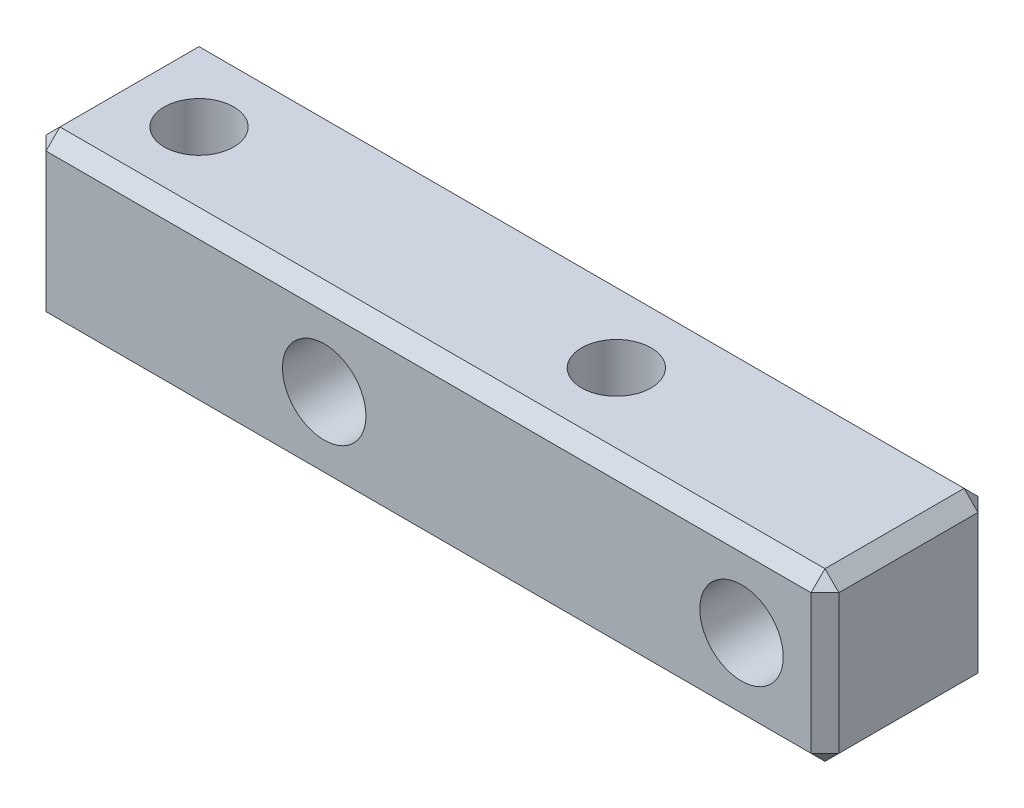
SolidWorks part; units mm, degrees
material "6061 合金"
ref_plane "前视基准面" through (0, 0, 0) normal (0, 0, 1) x (1, 0, 0)
ref_plane "上视基准面" through (0, 0, 0) normal (0, 1, 0) x (1, 0, 0)
ref_plane "右视基准面" through (0, 0, 0) normal (1, 0, 0) x (0, 0, -1)
sketch "草图2" plane through (0, 0, 0) normal (0, 0, 1) x (1, 0, 0)
  line L10 (3, 3) -> (3, -3)
  line L11 (0, 0) -> (-15, 0) construction
  line L41 (3, -3) -> (-25.5, -3)
  line L48 (-25.5, 3) -> (3, 3)
  line L49 (-25.5, 3) -> (-25.5, -3)
  circle A3 centre (-15, 0) radius 1.5
  circle A5 centre (0, 0) radius 1.5
  dimension "D1" = 15
  dimension "D2" = 3
  dimension "D3" = 3
  dimension "D4" = 10.5
  dimension "D7" = 3
  dimension "D6" = 3
extrude "凸台-拉伸1" add sketch "草图2" along normal mid plane 6
hole_wizard "M3 螺纹孔1" [suppressed] positions "草图5" profile "草图4" tap size "M3" standard "GB"
sketch "草图5" plane through (0, 0, 3) normal (0, 0, 1) x (1, 0, 0)
  point P0 (0, 0)
  point P3 (-15, 0)
sketch "草图4" plane through (0, 0, 3) normal (1, 0, 0) x (0, -1, 0)
  line L0 (0, 0) -> (0, 6)
  line L1 (0, 6) -> (1.25, 6)
  line L2 (1.25, 6) -> (1.25, 0)
  line L5 (1.25, 0) -> (0, 0)
  line L11 (0, -6.35) -> (0, 107.95) construction
  dimension "通孔螺纹孔钻头直径" = 2.5
  dimension "通孔螺纹孔钻头深度" = 6
hole_wizard "M3 螺纹孔2" positions "草图6" profile "草图7" tap size "M3" standard "GB" end condition through all
sketch "草图6" plane through (0, 3, 0) normal (0, 1, 0) x (1, 0, 0)
  line L1 (-22.5, 0) -> (0, 0) construction
  line L2 (-25.5, -3) -> (-25.5, 3) construction
  point P0 (-7.5, 0)
  point P2 (-22.5, 0)
  dimension "D1" = 3
  dimension "D2" = 15
sketch "草图7" plane through (-7.5, 3, 0) normal (1, 0, 0) x (0, 0, 1)
  line L0 (0, 0) -> (0, 6)
  line L1 (0, 6) -> (1.25, 6)
  line L2 (1.25, 6) -> (1.25, 0)
  line L5 (1.25, 0) -> (0, 0)
  line L11 (0, -6.35) -> (0, 107.95) construction
  dimension "通孔螺纹孔钻头直径" = 2.5
  dimension "通孔螺纹孔钻头深度" = 6
cosmetic thread "孔螺蚊线5" parameters "D2"=3
cosmetic thread "孔螺蚊线6" parameters "D2"=3
chamfer "倒角1" distance 0.5 angle 45 12 edges at (-11.25, -3, -3) (-11.25, -3, 3) (-25.5, 0, -3) (-25.5, 0, 3) (3, -3, 0) (3, 0, 3) (3, 0, -3) (-11.25, 3, -3) (3, 3, 0) (-11.25, 3, 3) (-25.5, 3, 0) (-25.5, -3, 0)
